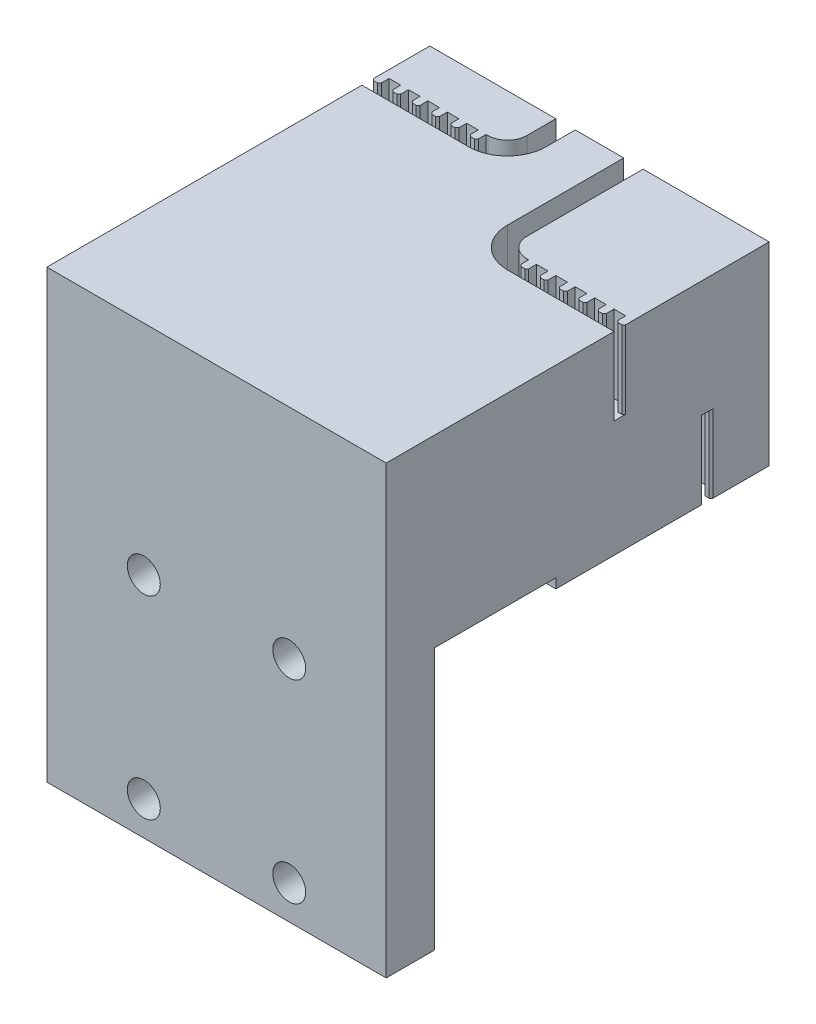
SolidWorks part; units mm, degrees
ref_plane "Front Plane" through (0, 0, 0) normal (0, 0, 1) x (1, 0, 0)
ref_plane "Top Plane" through (0, 0, 0) normal (0, 1, 0) x (1, 0, 0)
ref_plane "Right Plane" through (0, 0, 0) normal (1, 0, 0) x (0, 0, -1)
sketch "Sketch1" plane through (0, 0, 0) normal (0, 1, 0) x (1, 0, 0)
  line L1 (0, 0) -> (35, 0)
  line L2 (0, 0) -> (0, 22)
  line L3 (0, 22) -> (35, 22)
  line L4 (35, 0) -> (35, 22)
  dimension "D1" = 22
  dimension "D2" = 35
extrude "Boss-Extrude1" add sketch "Sketch1" along normal blind 20
sketch "Sketch2" plane through (0, 20, 0) normal (0, 1, 0) x (1, 0, 0)
  line L0 (0, 15) -> (11, 15)
  line L1 (0, 22) -> (0, 0) construction
  line L2 (15, 19) -> (15, 22)
  line L3 (35, 22) -> (0, 22) construction
  line L4 (0, 17) -> (11, 17)
  line L5 (13, 19) -> (13, 22)
  line L6 (35, 6) -> (24, 6)
  line L7 (35, 0) -> (35, 22) construction
  line L8 (20, 10) -> (20, 22)
  line L9 (0, 0) -> (35, 0) construction
  line L10 (22, 22) -> (22, 10)
  line L11 (24, 8) -> (35, 8)
  line L12 (35, 8) -> (35, 6)
  line L13 (0, 15) -> (0, 17)
  line L14 (13, 22) -> (15, 22)
  line L15 (20, 22) -> (22, 22)
  arc A0 (15, 19) -> (11, 15) centre (11, 19) cw
  arc A1 (13, 19) -> (11, 17) centre (11, 19) cw
  arc A2 (20, 10) -> (24, 6) centre (24, 10) ccw
  arc A3 (22, 10) -> (24, 8) centre (24, 10) ccw
  point P9 (15, 15)
  point P15 (13, 17)
  point P29 (20, 6)
  point P32 (22, 8)
  dimension "D3" = 4
  dimension "D6" = 2
  dimension "D11" = 4
  dimension "D12" = 2
  dimension "D1" = 15
  dimension "D2" = 7
  dimension "D4" = 5
  dimension "D5" = 13
  dimension "D7" = 15
  dimension "D8" = 6
  dimension "D9" = 13
  dimension "D10" = 2
extrude "Cut-Extrude1" cut sketch "Sketch2" against normal blind 8
sketch "Sketch5" plane through (0, 0, 0) normal (0, -1, 0) x (-1, 0, 0)
  line L0 (-35, 15) -> (-24, 15)
  line L2 (-20, 19) -> (-20, 22)
  line L4 (-35, 17) -> (-24, 17)
  line L5 (-22, 19) -> (-22, 22)
  line L6 (0, 6) -> (-11, 6)
  line L8 (-15, 10) -> (-15, 22)
  line L10 (-13, 22) -> (-13, 10)
  line L11 (-11, 8) -> (0, 8)
  line L12 (0, 8) -> (0, 6)
  line L13 (-35, 15) -> (-35, 17)
  line L14 (-22, 22) -> (-20, 22)
  line L15 (-15, 22) -> (-13, 22)
  line L16 (-35, 0) -> (-35, 22) construction
  line L17 (-35, 22) -> (0, 22) construction
  line L18 (0, 22) -> (0, 0) construction
  line L19 (0, 0) -> (-35, 0) construction
  arc A0 (-20, 19) -> (-24, 15) centre (-24, 19) cw
  arc A1 (-22, 19) -> (-24, 17) centre (-24, 19) cw
  arc A2 (-15, 10) -> (-11, 6) centre (-11, 10) ccw
  arc A3 (-13, 10) -> (-11, 8) centre (-11, 10) ccw
  point P9 (-20, 15)
  point P15 (-22, 17)
  point P29 (-15, 6)
  point P32 (-13, 8)
  dimension "D3" = 4
  dimension "D6" = 2
  dimension "D11" = 4
  dimension "D12" = 2
  dimension "D1" = 15
  dimension "D2" = 7
  dimension "D4" = 5
  dimension "D5" = 13
  dimension "D7" = 15
  dimension "D8" = 0
  dimension "D9" = 13
  dimension "D10" = 2
  dimension "D13" = 0
  dimension "D14" = 0
  dimension "D15" = 0
  dimension "D16" = 6
extrude "Cut-Extrude2" cut sketch "Sketch5" against normal blind 8
sketch "Sketch6" plane through (0, 20, 0) normal (0, 1, 0) x (1, 0, 0)
  line L0 (0.2, 16) -> (0, 16.2)
  line L1 (0, 17) -> (0.8, 17)
  line L2 (0, 17) -> (0, 16.2)
  line L3 (0.2, 16) -> (0.6, 16)
  line L4 (0.8, 17) -> (0.8, 16.2)
  line L5 (0.6, 16) -> (0.8, 16.2)
  line L6 (2.2, 16) -> (2, 16.2)
  line L7 (2, 17) -> (2.8, 17)
  line L8 (2, 17) -> (2, 16.2)
  line L9 (2.2, 16) -> (2.6, 16)
  line L10 (2.8, 17) -> (2.8, 16.2)
  line L11 (2.6, 16) -> (2.8, 16.2)
  line L12 (4.2, 16) -> (4, 16.2)
  line L13 (4, 17) -> (4.8, 17)
  line L14 (4, 17) -> (4, 16.2)
  line L15 (4.2, 16) -> (4.6, 16)
  line L16 (4.8, 17) -> (4.8, 16.2)
  line L17 (4.6, 16) -> (4.8, 16.2)
  line L18 (6.2, 16) -> (6, 16.2)
  line L19 (6, 17) -> (6.8, 17)
  line L20 (6, 17) -> (6, 16.2)
  line L21 (6.2, 16) -> (6.6, 16)
  line L22 (6.8, 17) -> (6.8, 16.2)
  line L23 (6.6, 16) -> (6.8, 16.2)
  line L24 (8.2, 16) -> (8, 16.2)
  line L25 (8, 17) -> (8.8, 17)
  line L26 (8, 17) -> (8, 16.2)
  line L27 (8.2, 16) -> (8.6, 16)
  line L28 (8.8, 17) -> (8.8, 16.2)
  line L29 (8.6, 16) -> (8.8, 16.2)
  line L30 (10.2, 16) -> (10, 16.2)
  line L31 (10, 17) -> (10.8, 17)
  line L32 (10, 17) -> (10, 16.2)
  line L33 (10.2, 16) -> (10.6, 16)
  line L34 (10.8, 17) -> (10.8, 16.2)
  line L35 (10.6, 16) -> (10.8, 16.2)
  line L36 (34.4, 7) -> (34.2, 7.2)
  line L37 (34.2, 8) -> (35, 8)
  line L38 (34.2, 8) -> (34.2, 7.2)
  line L39 (34.4, 7) -> (34.8, 7)
  line L40 (35, 8) -> (35, 7.2)
  line L41 (34.8, 7) -> (35, 7.2)
  line L42 (35, 8) -> (24, 8) construction
  line L43 (35, 6) -> (35, 8) construction
  line L44 (32.4, 7) -> (32.2, 7.2)
  line L45 (32.2, 8) -> (33, 8)
  line L46 (32.2, 8) -> (32.2, 7.2)
  line L47 (32.4, 7) -> (32.8, 7)
  line L48 (33, 8) -> (33, 7.2)
  line L49 (32.8, 7) -> (33, 7.2)
  line L50 (30.4, 7) -> (30.2, 7.2)
  line L51 (30.2, 8) -> (31, 8)
  line L52 (30.2, 8) -> (30.2, 7.2)
  line L53 (30.4, 7) -> (30.8, 7)
  line L54 (31, 8) -> (31, 7.2)
  line L55 (30.8, 7) -> (31, 7.2)
  line L56 (28.4, 7) -> (28.2, 7.2)
  line L57 (28.2, 8) -> (29, 8)
  line L58 (28.2, 8) -> (28.2, 7.2)
  line L59 (28.4, 7) -> (28.8, 7)
  line L60 (29, 8) -> (29, 7.2)
  line L61 (28.8, 7) -> (29, 7.2)
  line L62 (26.4, 7) -> (26.2, 7.2)
  line L63 (26.2, 8) -> (27, 8)
  line L64 (26.2, 8) -> (26.2, 7.2)
  line L65 (26.4, 7) -> (26.8, 7)
  line L66 (27, 8) -> (27, 7.2)
  line L67 (26.8, 7) -> (27, 7.2)
  line L68 (24.4, 7) -> (24.2, 7.2)
  line L69 (24.2, 8) -> (25, 8)
  line L70 (24.2, 8) -> (24.2, 7.2)
  line L71 (24.4, 7) -> (24.8, 7)
  line L72 (25, 8) -> (25, 7.2)
  line L73 (24.8, 7) -> (25, 7.2)
  dimension "D1" = 6
  dimension "D2" = 0.8
  dimension "D3" = 0.8
  dimension "D4" = 0
  dimension "D5" = 0
  dimension "D6" = 6
  dimension "D7" = 0.8
  dimension "D8" = 0.8
  dimension "D9" = 0.8
  dimension "D10" = 0.8
  dimension "D11" = 0.2
  dimension "D12" = 0.2
  dimension "D13" = 0.2
extrude "Boss-Extrude2" add sketch "Sketch6" against normal blind 8
sketch "Sketch8" plane through (0, 0, 0) normal (0, -1, 0) x (1, 0, 0)
  line L0 (35, -17) -> (35, -16.2)
  line L1 (35, -17) -> (35, -15) construction
  line L2 (35, -16.2) -> (34.8, -16)
  line L3 (34.8, -16) -> (34.4, -16)
  line L4 (34.4, -16) -> (34.2, -16.2)
  line L5 (34.2, -16.2) -> (34.2, -17)
  line L6 (34.2, -17) -> (35, -17)
  line L7 (33, -17) -> (33, -16.2)
  line L8 (33, -16.2) -> (32.8, -16)
  line L9 (32.8, -16) -> (32.4, -16)
  line L10 (32.4, -16) -> (32.2, -16.2)
  line L11 (32.2, -16.2) -> (32.2, -17)
  line L12 (32.2, -17) -> (33, -17)
  line L13 (31, -17) -> (31, -16.2)
  line L14 (31, -16.2) -> (30.8, -16)
  line L15 (30.8, -16) -> (30.4, -16)
  line L16 (30.4, -16) -> (30.2, -16.2)
  line L17 (30.2, -16.2) -> (30.2, -17)
  line L18 (30.2, -17) -> (31, -17)
  line L19 (29, -17) -> (29, -16.2)
  line L20 (29, -16.2) -> (28.8, -16)
  line L21 (28.8, -16) -> (28.4, -16)
  line L22 (28.4, -16) -> (28.2, -16.2)
  line L23 (28.2, -16.2) -> (28.2, -17)
  line L24 (28.2, -17) -> (29, -17)
  line L25 (27, -17) -> (27, -16.2)
  line L26 (27, -16.2) -> (26.8, -16)
  line L27 (26.8, -16) -> (26.4, -16)
  line L28 (26.4, -16) -> (26.2, -16.2)
  line L29 (26.2, -16.2) -> (26.2, -17)
  line L30 (26.2, -17) -> (27, -17)
  line L31 (25, -17) -> (25, -16.2)
  line L32 (25, -16.2) -> (24.8, -16)
  line L33 (24.8, -16) -> (24.4, -16)
  line L34 (24.4, -16) -> (24.2, -16.2)
  line L35 (24.2, -16.2) -> (24.2, -17)
  line L36 (24.2, -17) -> (25, -17)
  line L37 (0.8, -8) -> (0.8, -7.2)
  line L38 (0.8, -7.2) -> (0.6, -7)
  line L39 (0.6, -7) -> (0.2, -7)
  line L40 (0.2, -7) -> (0, -7.2)
  line L41 (0, -7.2) -> (0, -8)
  line L42 (0, -8) -> (0.8, -8)
  line L43 (0, -8) -> (11, -8) construction
  line L44 (2.8, -8) -> (2.8, -7.2)
  line L45 (2.8, -7.2) -> (2.6, -7)
  line L46 (2.6, -7) -> (2.2, -7)
  line L47 (2.2, -7) -> (2, -7.2)
  line L48 (2, -7.2) -> (2, -8)
  line L49 (2, -8) -> (2.8, -8)
  line L50 (4.8, -8) -> (4.8, -7.2)
  line L51 (4.8, -7.2) -> (4.6, -7)
  line L52 (4.6, -7) -> (4.2, -7)
  line L53 (4.2, -7) -> (4, -7.2)
  line L54 (4, -7.2) -> (4, -8)
  line L55 (4, -8) -> (4.8, -8)
  line L56 (6.8, -8) -> (6.8, -7.2)
  line L57 (6.8, -7.2) -> (6.6, -7)
  line L58 (6.6, -7) -> (6.2, -7)
  line L59 (6.2, -7) -> (6, -7.2)
  line L60 (6, -7.2) -> (6, -8)
  line L61 (6, -8) -> (6.8, -8)
  line L62 (8.8, -8) -> (8.8, -7.2)
  line L63 (8.8, -7.2) -> (8.6, -7)
  line L64 (8.6, -7) -> (8.2, -7)
  line L65 (8.2, -7) -> (8, -7.2)
  line L66 (8, -7.2) -> (8, -8)
  line L67 (8, -8) -> (8.8, -8)
  line L68 (10.8, -8) -> (10.8, -7.2)
  line L69 (10.8, -7.2) -> (10.6, -7)
  line L70 (10.6, -7) -> (10.2, -7)
  line L71 (10.2, -7) -> (10, -7.2)
  line L72 (10, -7.2) -> (10, -8)
  line L73 (10, -8) -> (10.8, -8)
  dimension "D1" = 0.8
  dimension "D2" = 0.2
  dimension "D3" = 0.8
  dimension "D4" = 0.8
  dimension "D5" = 0.2
  dimension "D6" = 6
  dimension "D7" = 0.8
  dimension "D8" = 0.2
  dimension "D9" = 0.8
  dimension "D10" = 0.8
  dimension "D11" = 0.2
  dimension "D12" = 0
  dimension "D13" = 0
  dimension "D14" = 6
extrude "Boss-Extrude4" add sketch "Sketch8" against normal blind 8
sketch "Sketch9" plane through (0, 0, 0) normal (0, 0, 1) x (1, 0, 0)
  line L1 (0, 20) -> (35, 20)
  line L2 (0, 20) -> (0, 1)
  line L3 (0, 1) -> (35, 1)
  line L4 (35, 20) -> (35, 1)
  line L5 (35, 20) -> (35, 0) construction
  dimension "D1" = 19
  dimension "D2" = 35
extrude "Boss-Extrude5" add sketch "Sketch9" along normal blind 12.5
sketch "Sketch11" plane through (0, 0, 12.5) normal (0, 0, 1) x (1, 0, 0)
  line L1 (0, 20) -> (35, 20)
  line L2 (0, 20) -> (0, -26)
  line L3 (0, -26) -> (35, -26)
  line L4 (35, 20) -> (35, -26)
  dimension "D1" = 46
  dimension "D2" = 35
extrude "Boss-Extrude6" add sketch "Sketch11" along normal blind 5
sketch "Sketch12" plane through (0, 0, 17.5) normal (0, 0, 1) x (1, 0, 0)
  line L0 (0, 20) -> (0, -26) construction
  line L1 (0, -26) -> (35, -26) construction
  line L3 (35, 20) -> (0, 20) construction
  circle A0 centre (10, -2.5) radius 1.7
  circle A1 centre (25, -2.5) radius 1.7
  circle A2 centre (25, -22.5) radius 1.7
  circle A3 centre (10, -22.5) radius 1.7
  point P0 (17.5, -12.5)
  dimension "D3" = 3.4
  dimension "D4" = 7.5
  dimension "D1" = 17.5
  dimension "D2" = 13.5
  dimension "D5" = 10
  dimension "D7" = 46
  dimension "D6" = 2
extrude "Cut-Extrude3" cut sketch "Sketch12" against normal blind 5
